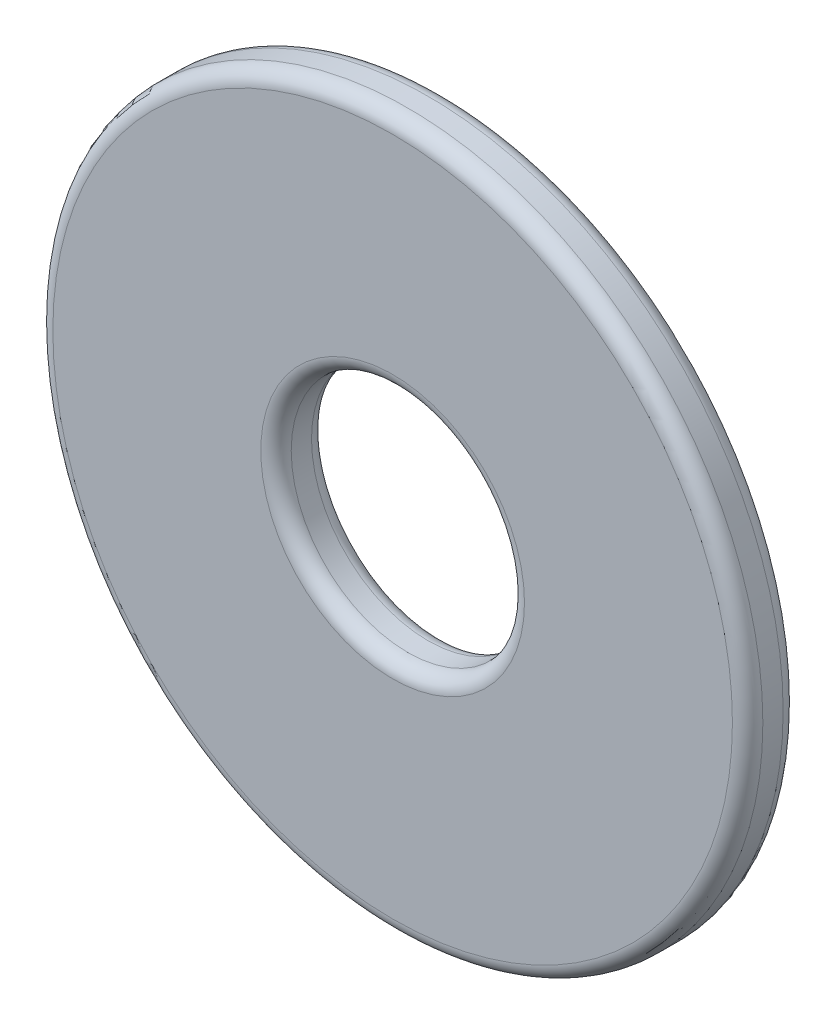
SolidWorks part; units mm, degrees
material "Brass"
ref_plane "Frontal" through (0, 0, 0) normal (0, 0, 1) x (1, 0, 0)
ref_plane "Superior" through (0, 0, 0) normal (0, 1, 0) x (1, 0, 0)
ref_plane "Direito" through (0, 0, 0) normal (1, 0, 0) x (0, 0, -1)
sketch "Sketch1" plane through (0, 0, 0) normal (0, 0, 1) x (1, 0, 0)
  circle A0 centre (0, 0) radius 3.5
  circle A1 centre (0, 0) radius 1.15
  dimension "D1" = 7
  dimension "D2" = 2.3
extrude "Extrude1" add sketch "Sketch1" along normal mid plane 0.5
fillet "Fillet1" radius 0.15 4 edges at (1.15, 0, -0.25) (1.15, 0, 0.25) (3.5, 0, -0.25) (3.5, 0, 0.25)
